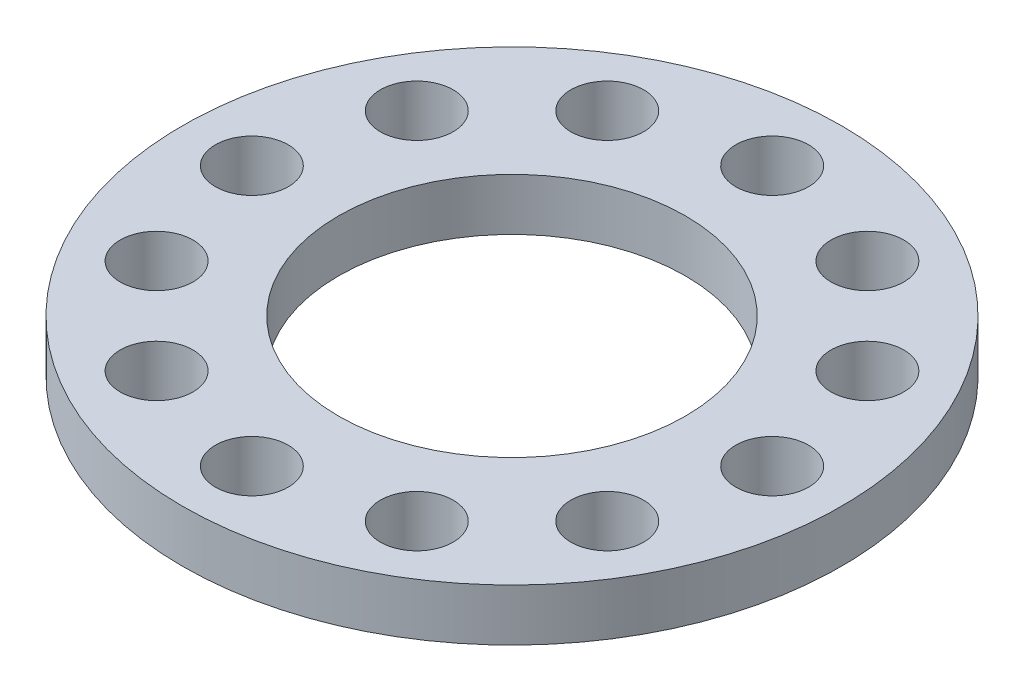
SolidWorks part; units mm, degrees
material "5052-O"
ref_plane "正面" through (0, 0, 0) normal (0, 0, 1) x (1, 0, 0)
ref_plane "平面" through (0, 0, 0) normal (0, 1, 0) x (1, 0, 0)
ref_plane "右側面" through (0, 0, 0) normal (1, 0, 0) x (0, 0, -1)
sketch "ｽｹｯﾁ1" plane through (0, 0, 0) normal (0, 1, 0) x (1, 0, 0)
  circle A0 centre (0, 0) radius 19
extrude "ﾎﾞｽ - 押し出し1" add sketch "ｽｹｯﾁ1" along normal blind 3
sketch "ｽｹｯﾁ2" plane through (0, 3, 0) normal (0, 1, 0) x (1, 0, 0)
  circle A0 centre (0, 15) radius 2.1
  circle A1 centre (7.5, 12.9904) radius 2.1
  circle A2 centre (12.9904, 7.5) radius 2.1
  circle A3 centre (15, 0) radius 2.1
  circle A4 centre (12.9904, -7.5) radius 2.1
  circle A5 centre (7.5, -12.9904) radius 2.1
  circle A6 centre (0, -15) radius 2.1
  circle A7 centre (-7.5, -12.9904) radius 2.1
  circle A8 centre (-12.9904, -7.5) radius 2.1
  circle A9 centre (-15, 0) radius 2.1
  circle A10 centre (-12.9904, 7.5) radius 2.1
  circle A11 centre (-7.5, 12.9904) radius 2.1
  point P27 (0, 0)
  dimension "D1" = 12
extrude "ｶｯﾄ - 押し出し1" cut sketch "ｽｹｯﾁ2" against normal up to next
sketch "ｽｹｯﾁ3" plane through (0, 3, 0) normal (0, 1, 0) x (1, 0, 0)
  circle A0 centre (0, 0) radius 10
extrude "ｶｯﾄ - 押し出し2" cut sketch "ｽｹｯﾁ3" against normal up to next
